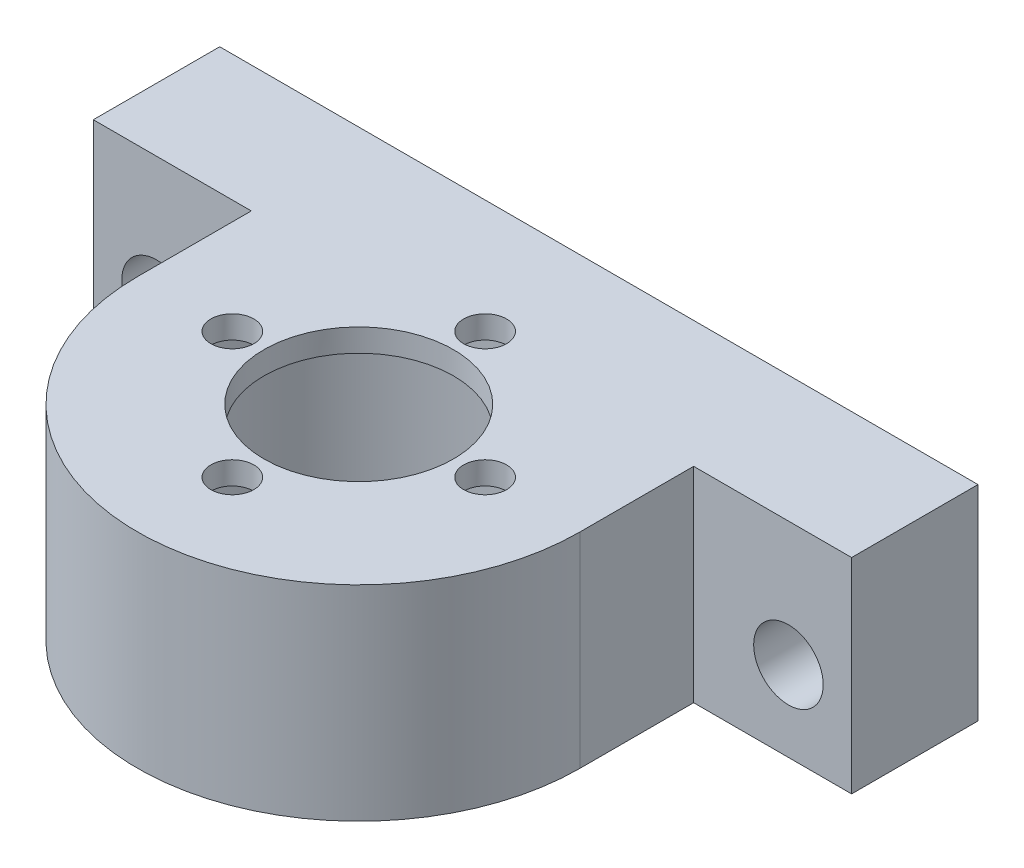
SolidWorks part; units mm, degrees
ref_plane "Front Plane" through (0, 0, 0) normal (0, 0, 1) x (1, 0, 0)
ref_plane "Top Plane" through (0, 0, 0) normal (0, 1, 0) x (1, 0, 0)
ref_plane "Right Plane" through (0, 0, 0) normal (1, 0, 0) x (0, 0, -1)
sketch "Sketch2" plane through (0, 0, 0) normal (0, 1, 0) x (1, 0, 0)
  line L0 (0, 0) -> (0, 28.7844) construction
  line L1 (30, 9) -> (-30, 9)
  line L2 (-30, 9) -> (-30, 19)
  line L3 (-30, 19) -> (30, 19)
  line L4 (30, 9) -> (30, 19)
  line L5 (17.5, 0) -> (17.5, 9)
  line L6 (-17.5, 0) -> (-17.5, 9)
  circle A0 centre (0, 0) radius 13
  circle A1 centre (0, 0) radius 17.5
  point P10 (0, 19)
  point P11 (0, 9)
  dimension "D1" = 26
  dimension "D2" = 35
  dimension "D3" = 9
  dimension "D4" = 30
  dimension "D5" = 10
extrude "Boss-Extrude1" add sketch "Sketch2" along normal blind 12.7 contours A1 L5 L1 | L0 A1 L1 L4 L3 | L0 A0 L1 A1 | A1 L1 A0 | A0 L0 A1 L1 | A1 L1 L6 | A1 L0 L3 L2 L1
sketch "Sketch4" plane through (0, 0, -19) normal (0, 0, -1) x (-1, 0, 0)
  line L0 (0, 0) -> (0, 12.7) construction
  line L1 (30, 12.7) -> (-30, 12.7) construction
  line L2 (30, 6.35) -> (-30, 6.35) construction
  line L3 (30, 12.7) -> (30, 0) construction
  line L4 (-30, 12.7) -> (-30, 0) construction
  point P11 (25, 6.35)
  point P13 (-25, 6.35)
  point P15 (0, 6.35)
  dimension "D1" = 5
hole_wizard "M5 Clearance Hole1" positions "3DSketch1" profile "Sketch5" hole size "M5" standard "ANSI Metric"
sketch3d "3DSketch1"
  point P0 (-25, 6.35, -19)
  point P3 (25, 6.35, -19)
sketch "Sketch5" plane through (-25, 6.35, -19) normal (1, 0, 0) x (0, 1, 0)
  line L0 (0, 0) -> (0, 11.7524)
  line L1 (0, 11.7524) -> (2.75, 10.1)
  line L2 (2.75, 10.1) -> (2.75, 0)
  line L5 (2.75, 0) -> (0, 0)
  line L10 (0, 11.7524) -> (-2.75, 10.1) construction
  line L11 (0, -6.35) -> (0, 107.95) construction
  dimension "Hole Dia." = 5.5
  dimension "Hole Depth" = 10.1
  dimension "Drill Angle" = 118
sketch "Sketch9" plane through (0, 12.7, 0) normal (0, 1, 0) x (1, 0, 0)
  line L7 (-30, 9) -> (-17.5, 9)
  line L8 (-17.5, 9) -> (-17.5, 0)
  line L9 (17.5, 0) -> (17.5, 9)
  line L10 (17.5, 9) -> (30, 9)
  line L11 (30, 9) -> (30, 19)
  line L12 (30, 19) -> (-30, 19)
  line L13 (-30, 19) -> (-30, 9)
  line L14 (-30, 9) -> (-17.5, 9)
  line L15 (-17.5, 9) -> (-17.5, 0)
  line L16 (17.5, 0) -> (17.5, 9)
  line L17 (17.5, 9) -> (30, 9)
  line L18 (30, 9) -> (30, 19)
  line L19 (30, 19) -> (-30, 19)
  line L20 (-30, 19) -> (-30, 9)
  arc A1 (-17.5, 0) -> (17.5, 0) centre (0, 0) ccw
  arc A2 (-17.5, 0) -> (17.5, 0) centre (0, 0) ccw
  dimension "D1" = 0
extrude "Boss-Extrude2" add sketch "Sketch9" along normal blind 3.5
sketch "Sketch10" plane through (0, 12.7, 0) normal (0, -1, 0) x (1, 0, 0)
  circle A0 centre (0, 0) radius 13
extrude "Cut-Extrude1" cut sketch "Sketch10" against normal blind 1.7
sketch "Sketch11" plane through (0, 16.2, 0) normal (0, 1, 0) x (1, 0, 0)
  circle A0 centre (0, 0) radius 7.5
  dimension "D1" = 15
extrude "Cut-Extrude2" cut sketch "Sketch11" against normal through all
sketch "Sketch12" plane through (0, 16.2, 0) normal (0, 1, 0) x (1, 0, 0)
  line L0 (0, 0) -> (0, 10) construction
  circle A0 centre (0, 0) radius 10 construction
  point P5 (0, 10)
  point P8 (10, 0)
  point P9 (0, -10)
  point P10 (-10, 0)
  dimension "D1" = 20
  dimension "D3" = 10
  dimension "D4" = 10
  dimension "D2" = 4
hole_wizard "M3 Clearance Hole1" positions "3DSketch3" profile "Sketch14" hole size "M3" standard "ANSI Metric"
sketch3d "3DSketch3"
  point P0 (-10, 16.2, 0)
  point P3 (0, 16.2, 10)
  point P6 (10, 16.2, 0)
  point P9 (0, 16.2, -10)
sketch "Sketch14" plane through (-10, 16.2, 0) normal (1, 0, 0) x (0, 0, 1)
  line L0 (0, 0) -> (0, 8.5215)
  line L1 (0, 8.5215) -> (1.7, 7.5)
  line L2 (1.7, 7.5) -> (1.7, 0)
  line L5 (1.7, 0) -> (0, 0)
  line L10 (0, 8.5215) -> (-1.7, 7.5) construction
  line L11 (0, -6.35) -> (0, 107.95) construction
  dimension "Hole Dia." = 3.4
  dimension "Hole Depth" = 7.5
  dimension "Drill Angle" = 118
